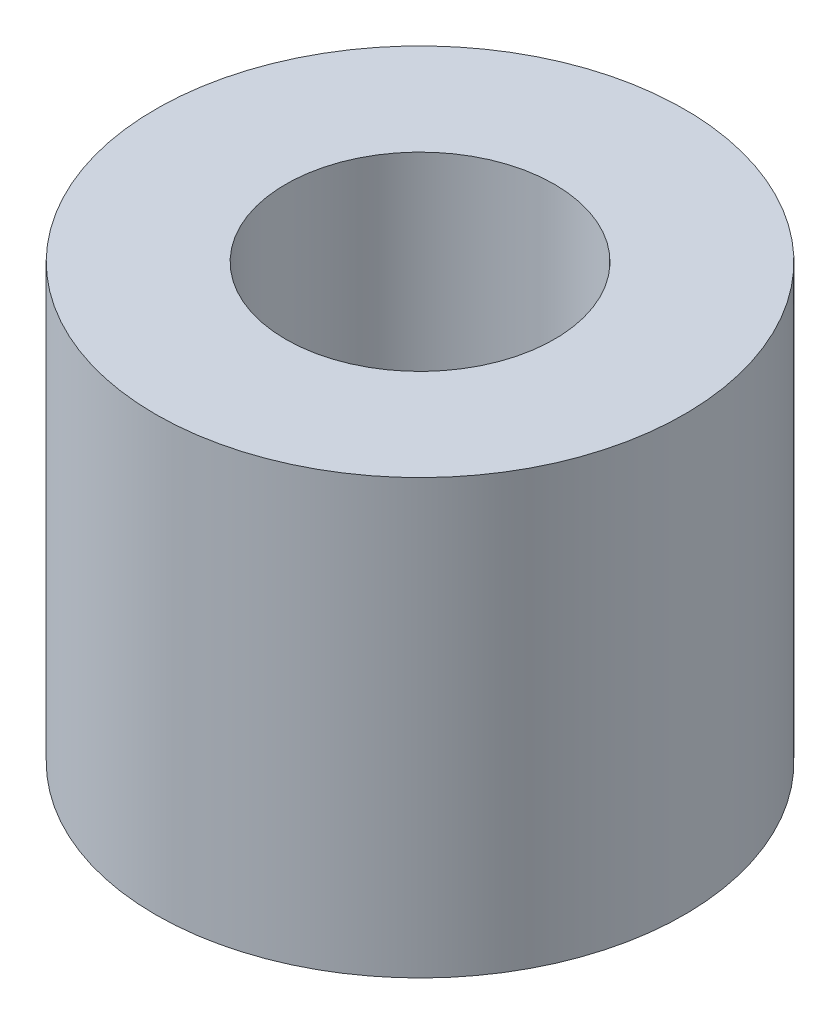
SolidWorks part; units mm, degrees
ref_plane "Front Plane" through (0, 0, 0) normal (0, 0, 1) x (1, 0, 0)
ref_plane "Top Plane" through (0, 0, 0) normal (0, 1, 0) x (1, 0, 0)
ref_plane "Right Plane" through (0, 0, 0) normal (1, 0, 0) x (0, 0, -1)
sketch "Sketch1" plane through (0, 0, 0) normal (0, 1, 0) x (1, 0, 0)
  circle A0 centre (0, 0) radius 1.55
  circle A1 centre (0, 0) radius 3.05
  dimension "D1" = 3.1
  dimension "D2" = 1.5
extrude "Boss-Extrude1" add sketch "Sketch1" along normal blind 5
